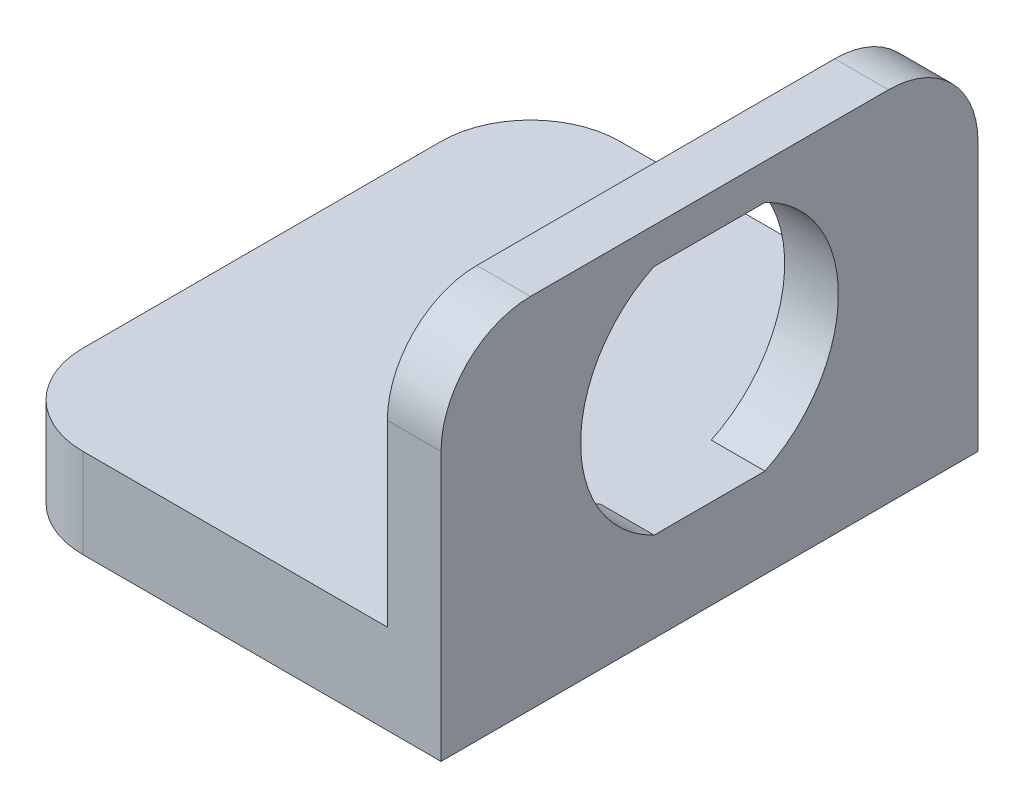
SolidWorks part; units mm, degrees
ref_plane "Front Plane" through (0, 0, 0) normal (0, 0, 1) x (1, 0, 0)
ref_plane "Top Plane" through (0, 0, 0) normal (0, 1, 0) x (1, 0, 0)
ref_plane "Right Plane" through (0, 0, 0) normal (1, 0, 0) x (0, 0, -1)
sketch "Sketch1" plane through (0, 0, 0) normal (0, 0, 1) x (1, 0, 0)
  line L0 (0, 0) -> (0, 25.4)
  line L1 (0, 25.4) -> (-3.81, 25.4)
  line L2 (-3.81, 25.4) -> (-3.81, 6.35)
  line L3 (-3.81, 6.35) -> (-31.75, 6.35)
  line L4 (-31.75, 6.35) -> (-31.75, 0)
  line L5 (-31.75, 0) -> (0, 0)
  dimension "D1" = 6.35
  dimension "D2" = 3.81
  dimension "D3" = 31.75
  dimension "D4" = 25.4
extrude "Boss-Extrude1" add sketch "Sketch1" along normal blind 38.1
hole_wizard "1/4-20 Tapped Hole1" positions "Sketch3" profile "Sketch2" tap size "1/4-20" standard "ANSI Inch" end condition through all
sketch "Sketch3" plane through (0, 6.35, 0) normal (0, 1, 0) x (1, 0, 0)
  line L0 (-31.75, -19.05) -> (-16.51, -19.05) construction
  line L1 (-31.75, -38.1) -> (-31.75, 0) construction
  line L3 (-3.81, -38.1) -> (-3.81, 0) construction
  point P0 (-16.51, -19.05)
  dimension "D1" = 12.7
sketch "Sketch2" plane through (-16.51, 6.35, 19.05) normal (1, 0, 0) x (0, 0, 1)
  line L0 (0, 0) -> (0, 6.35)
  line L1 (0, 6.35) -> (2.5527, 6.35)
  line L2 (2.5527, 6.35) -> (2.5527, 0)
  line L5 (2.5527, 0) -> (0, 0)
  line L11 (0, -6.35) -> (0, 107.95) construction
  dimension "Thru Tap Drill Dia." = 5.1054
  dimension "Thru Tap Drill Depth" = 6.35
cosmetic thread "Hole Thread1" parameters "D2"=6.35
sketch "Sketch4" plane through (0, 0, 0) normal (1, 0, 0) x (0, 0, -1)
  line L0 (-19.05, 14.605) -> (-19.05, 25.4) construction
  line L1 (-38.1, 25.4) -> (0, 25.4) construction
  line L2 (-22.9829, 22.86) -> (-15.1171, 22.86)
  line L3 (-38.1, 6.35) -> (0, 6.35) construction
  line L4 (-15.1171, 6.35) -> (-22.9829, 6.35)
  arc A0 (-22.9829, 22.86) -> (-22.9829, 6.35) centre (-19.05, 14.605) ccw
  arc A1 (-15.1171, 6.35) -> (-15.1171, 22.86) centre (-19.05, 14.605) ccw
  dimension "D1" = 18.288
  dimension "D2" = 16.51
extrude "Cut-Extrude1" cut sketch "Sketch4" against normal through all
fillet "Fillet1" radius 6.35 4 edges at (-31.75, 3.175, 0) (-31.75, 3.175, 38.1) (-1.905, 25.4, 0) (-1.905, 25.4, 38.1)
